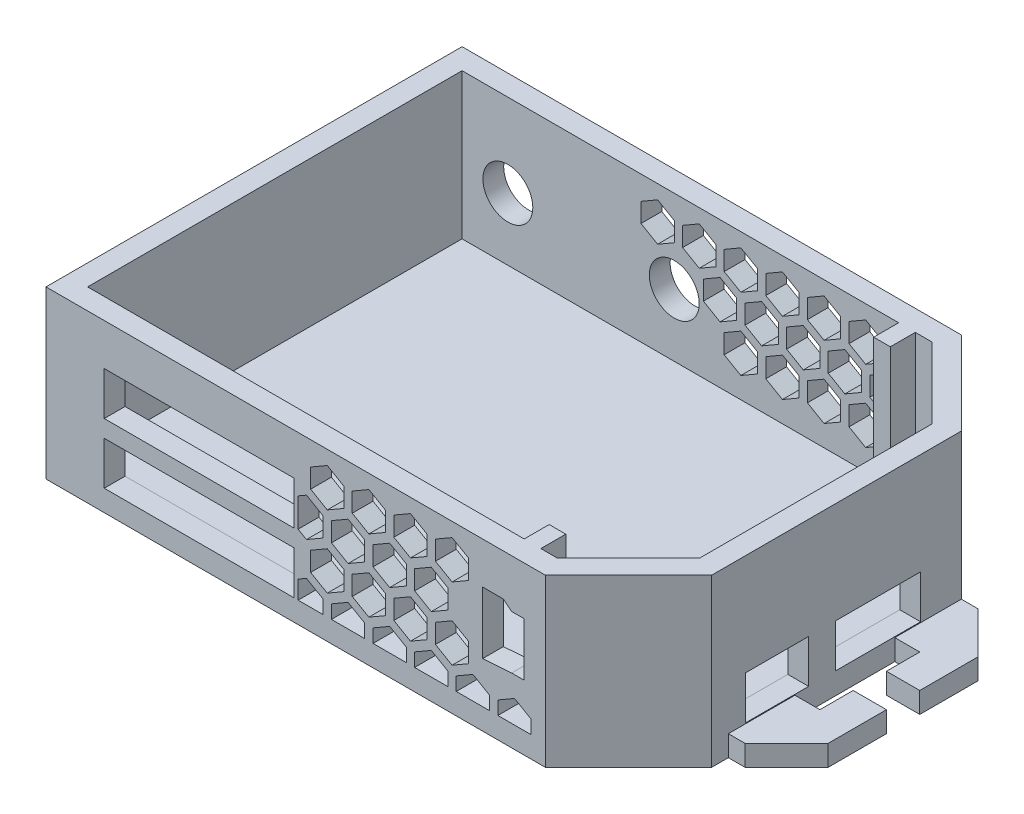
SolidWorks part; units mm, degrees
ref_plane "Front Plane" through (0, 0, 0) normal (0, 0, 1) x (1, 0, 0)
ref_plane "Top Plane" through (0, 0, 0) normal (0, 1, 0) x (1, 0, 0)
ref_plane "Right Plane" through (0, 0, 0) normal (1, 0, 0) x (0, 0, -1)
sketch "Sketch1" plane through (0, 0, 0) normal (0, 1, 0) x (1, 0, 0)
  line L1 (-35, 25) -> (35, 25)
  line L2 (-35, 25) -> (-35, -25)
  line L3 (-35, -25) -> (35, -25)
  line L4 (35, 25) -> (35, -25)
  line L5 (0, -25) -> (0, 25) construction
  line L6 (-35, 0) -> (35, 0) construction
  point P0 (0, 0)
  dimension "D1" = 70
  dimension "D2" = 50
extrude "Boss-Extrude1" add sketch "Sketch1" along normal blind 20
chamfer "Chamfer2" distance 10 angle 45 2 edges at (35, 10, 25) (35, 10, -25)
shell "Shell3" thickness 2.5
sketch "Sketch2" plane through (0, 0, -25) normal (0, 0, -1) x (-1, 0, 0)
  line L0 (-25, 0) -> (35, 0) construction
  line L1 (35, 20) -> (35, 0) construction
  circle A0 centre (27, 10) radius 3
  dimension "D1" = 6
  dimension "D2" = 10
  dimension "D3" = 8
extrude "Cut-Extrude1" cut sketch "Sketch2" against normal blind 20
sketch "Sketch3" plane through (0, 0, -22.5) normal (0, 0, 1) x (1, 0, 0)
  line L0 (23.9645, 2.5) -> (-32.5, 2.5) construction
  line L1 (21.9645, 2.5) -> (19.9645, 2.5)
  line L2 (21.9645, 2.5) -> (21.9645, 20)
  line L3 (21.9645, 20) -> (19.9645, 20)
  line L4 (19.9645, 2.5) -> (19.9645, 20)
  line L5 (23.9645, 20) -> (-32.5, 20) construction
  line L6 (23.9645, 20) -> (23.9645, 2.5) construction
  dimension "D1" = 2
  dimension "D2" = 2
extrude "Boss-Extrude2" add sketch "Sketch3" along normal blind 3
sketch "Sketch4" plane through (0, 0, 22.5) normal (0, 0, -1) x (-1, 0, 0)
  line L0 (32.5, 2.5) -> (-23.9645, 2.5) construction
  line L1 (-21.9645, 2.5) -> (-19.9645, 2.5)
  line L2 (-21.9645, 2.5) -> (-21.9645, 6.5)
  line L3 (-21.9645, 6.5) -> (-19.9645, 6.5)
  line L4 (-19.9645, 2.5) -> (-19.9645, 6.5)
  line L5 (-23.9645, 2.5) -> (-23.9645, 20) construction
  point P6 (-21.9645, 4.5)
  dimension "D1" = 2
  dimension "D2" = 4
  dimension "D3" = 2
extrude "Boss-Extrude3" add sketch "Sketch4" along normal blind 3
sketch "Sketch6" plane through (0, 0, 22.5) normal (0, 0, -1) x (-1, 0, 0)
  line L0 (32.5, 20) -> (-23.9645, 20) construction
  line L1 (-19.9645, 20) -> (-21.9645, 20)
  line L2 (-19.9645, 20) -> (-19.9645, 16)
  line L3 (-19.9645, 16) -> (-21.9645, 16)
  line L4 (-21.9645, 20) -> (-21.9645, 16)
  dimension "D1" = 4
  dimension "D2" = 2
  dimension "D3" = 2
extrude "Boss-Extrude4" add sketch "Sketch6" along normal blind 3
sketch "Sketch9" plane through (0, 0, 25) normal (0, 0, 1) x (1, 0, 0)
  line L0 (19.5, 14.5) -> (18.5, 13.7)
  line L1 (22, 14.5) -> (17, 14.5)
  line L2 (22, 14.5) -> (22, 6.5)
  line L3 (22, 6.5) -> (17, 6.5)
  line L4 (17, 14.5) -> (17, 6.5)
  line L5 (18.5, 13.7) -> (17, 13.7)
  line L6 (19.5, 6.5) -> (18.5, 7.3)
  line L7 (18.5, 7.3) -> (17, 7.3)
  line L8 (-35, 0) -> (25, 0) construction
  line L9 (25, 0) -> (25, 20) construction
  point P10 (6.2655, 14.9626)
  point P12 (6.4121, 6.9626)
  dimension "D1" = 8
  dimension "D2" = 5
  dimension "D3" = 0.8
  dimension "D4" = 0.8
  dimension "D5" = 1.5
  dimension "D6" = 1.5
  dimension "D7" = 1
  dimension "D8" = 1
  dimension "D9" = 6.5
  dimension "D10" = 3
sketch "Sketch10" plane through (0, 0, 22.5) normal (0, 0, -1) x (-1, 0, 0)
  line L0 (-19.9645, 15) -> (-20.9645, 14.2)
  line L1 (-17.4645, 15) -> (-22.4645, 15)
  line L2 (-17.4645, 15) -> (-17.4645, 7)
  line L3 (-17.4645, 7) -> (-22.4645, 7)
  line L4 (-22.4645, 15) -> (-22.4645, 7)
  line L5 (-20.9645, 14.2) -> (-22.4645, 14.2)
  line L6 (-9.9645, 7) -> (-20.9645, 7.8)
  line L7 (-20.9645, 7.8) -> (-22.4645, 7.8)
  line L9 (-19.9645, 2.5) -> (-19.9645, 6.5) construction
  point P6 (-9.9645, 7)
  point P10 (-5.6953, 16.1153)
  point P12 (-5.5488, 8.1153)
  dimension "D1" = 8
  dimension "D2" = 5
  dimension "D3" = 0.8
  dimension "D4" = 0.8
  dimension "D5" = 1.5
  dimension "D6" = 1.5
  dimension "D7" = 1
  dimension "D9" = 2.5
  dimension "D10" = 0.5
extrude "Cut-Extrude4" cut sketch "Sketch10" against normal blind 3 contours L7 L6 L3 L2 L1 L0 L5 L4
sketch "Sketch11" plane through (0, 0, 25) normal (0, 0, 1) x (1, 0, 0)
  line L0 (-35, 20) -> (-35, 0) construction
  line L1 (-28, 15) -> (-5.2, 15)
  line L2 (-28, 15) -> (-28, 9.8)
  line L3 (-28, 9.8) -> (-5.2, 9.8)
  line L4 (-5.2, 15) -> (-5.2, 9.8)
  line L5 (-35, 20) -> (25, 20) construction
  line L6 (-28, 12.4) -> (-5.2, 12.4) construction
  line L7 (-28, 7.746) -> (-5.2, 7.746)
  line L8 (-28, 7.746) -> (-28, 2.546)
  line L9 (-28, 2.546) -> (-5.2, 2.546)
  line L10 (-5.2, 7.746) -> (-5.2, 2.546)
  line L11 (-28, 5.146) -> (-5.2, 5.146) construction
  point P8 (-5, 20)
  dimension "D1" = 22.8
  dimension "D2" = 5.2
  dimension "D3" = 7
  dimension "D4" = 5
  dimension "D5" = 5.2
  dimension "D6" = 7.254
  dimension "D7" = 22.8
  dimension "D8" = 7
extrude "Cut-Extrude5" cut sketch "Sketch11" against normal blind 4
sketch "Sketch12" plane through (35, 0, 0) normal (1, 0, 0) x (0, 0, -1)
  line L0 (-15, 0) -> (15, 0) construction
  line L1 (-10.9521, 7.8) -> (-3.3521, 7.8)
  line L2 (-10.9521, 7.8) -> (-10.9521, 2.6)
  line L3 (-10.9521, 2.6) -> (-3.3521, 2.6)
  line L4 (-3.3521, 7.8) -> (-3.3521, 2.6)
  dimension "D1" = 2.6
  dimension "D2" = 7.6
  dimension "D3" = 5.2
extrude "Cut-Extrude6" cut sketch "Sketch12" against normal blind 4
sketch "Sketch13" plane through (35, 0, 0) normal (1, 0, 0) x (0, 0, -1)
  line L0 (-3.3521, 2.6) -> (-3.3521, 7.8) construction
  line L1 (-0.1021, 7.8) -> (10.0979, 7.8)
  line L2 (-0.1021, 7.8) -> (-0.1021, 2.6)
  line L3 (-0.1021, 2.6) -> (10.0979, 2.6)
  line L4 (10.0979, 7.8) -> (10.0979, 2.6)
  line L5 (-15, 0) -> (15, 0) construction
  dimension "D1" = 3.25
  dimension "D2" = 5.2
  dimension "D3" = 2.6
  dimension "D4" = 10.2
extrude "Cut-Extrude7" cut sketch "Sketch13" against normal blind 4
sketch "Sketch18" plane through (-35, 0, 0) normal (-1, 0, 0) x (0, 0, 1)
  line L0 (-25, 0) -> (25, 0) construction
  line L1 (-15, 0) -> (-7, 0)
  line L2 (-15, 0) -> (-15, 2.5)
  line L3 (-15, 2.5) -> (-7, 2.5)
  line L4 (-7, 0) -> (-7, 2.5)
  line L5 (-25, 20) -> (-25, 0) construction
  line L7 (5, 0) -> (13, 0)
  line L8 (5, 0) -> (5, 2.5)
  line L9 (5, 2.5) -> (13, 2.5)
  line L10 (13, 0) -> (13, 2.5)
  point P12 (-7, 1.25)
  dimension "D1" = 2.5
  dimension "D2" = 8
  dimension "D3" = 10
  dimension "D4" = 8
  dimension "D5" = 12
extrude "Boss-Extrude5" add sketch "Sketch18" along normal blind 7
sketch "Sketch19" plane through (0, 0, -7) normal (0, 0, 1) x (1, 0, 0)
  line L0 (-42, 0) -> (-35, 0) construction
  line L1 (-42, 2.5) -> (-38, 2.5)
  line L2 (-42, 2.5) -> (-42, 0)
  line L3 (-42, 0) -> (-38, 0)
  line L4 (-38, 2.5) -> (-38, 0)
  dimension "D1" = 4
extrude "Boss-Extrude6" add sketch "Sketch19" along normal blind 4
sketch "Sketch20" plane through (0, 0, 5) normal (0, 0, -1) x (-1, 0, 0)
  line L0 (42, 2.5) -> (35, 2.5) construction
  line L1 (42, 0) -> (38, 0)
  line L2 (42, 0) -> (42, 2.5)
  line L3 (42, 2.5) -> (38, 2.5)
  line L4 (38, 0) -> (38, 2.5)
  dimension "D1" = 4
extrude "Boss-Extrude7" add sketch "Sketch20" along normal blind 4
chamfer "Chamfer3" distance 5 angle 45 2 edges at (-42, 1.25, -15) (-42, 1.25, 13)
sketch "Sketch23" plane through (35, 0, 0) normal (1, 0, 0) x (0, 0, -1)
  line L1 (-13, 0) -> (-5, 0)
  line L2 (-13, 0) -> (-13, 2.5)
  line L3 (-13, 2.5) -> (-5, 2.5)
  line L4 (-5, 0) -> (-5, 2.5)
  line L6 (25, 20) -> (25, 0) construction
  line L7 (7, 0) -> (15, 0)
  line L8 (7, 0) -> (7, 2.5)
  line L9 (7, 2.5) -> (15, 2.5)
  line L10 (15, 0) -> (15, 2.5)
  line L11 (-15, 0) -> (15, 0) construction
  point P4 (0, 0)
  point P12 (-5, 1.25)
  dimension "D1" = 2.5
  dimension "D2" = 8
  dimension "D3" = 10
  dimension "D4" = 8
  dimension "D5" = 12
  dimension "D6" = 2.5
  dimension "D7" = 0
extrude "Boss-Extrude8" add sketch "Sketch23" along normal blind 7
sketch "Sketch24" plane through (0, 0, -7) normal (0, 0, 1) x (1, 0, 0)
  line L0 (42, 2.5) -> (35, 2.5) construction
  line L1 (42, 0) -> (38, 0)
  line L2 (42, 0) -> (42, 2.5)
  line L3 (42, 2.5) -> (38, 2.5)
  line L4 (38, 0) -> (38, 2.5)
  dimension "D1" = 4
extrude "Boss-Extrude10" add sketch "Sketch24" along normal blind 4
sketch "Sketch25" plane through (0, 0, 5) normal (0, 0, -1) x (-1, 0, 0)
  line L0 (-42, 0) -> (-35, 0) construction
  line L1 (-42, 2.5) -> (-38, 2.5)
  line L2 (-42, 2.5) -> (-42, 0)
  line L3 (-42, 0) -> (-38, 0)
  line L4 (-38, 2.5) -> (-38, 0)
  dimension "D1" = 4
extrude "Boss-Extrude11" add sketch "Sketch25" along normal blind 4
chamfer "Chamfer4" distance 5 angle 45 2 edges at (42, 1.25, 13) (42, 1.25, -15)
sketch "Sketch26" plane through (0, 0, -25) normal (0, 0, -1) x (-1, 0, 0)
  line L0 (27, 10) -> (32.4685, 10) construction
  circle A0 centre (7, 10) radius 3
  dimension "D1" = 6
  dimension "D2" = 20
extrude "Cut-Extrude10" cut sketch "Sketch26" against normal blind 4
sketch "Sketch27" plane through (0, 0, 25) normal (0, 0, 1) x (1, 0, 0)
  line L2 (-35, 20) -> (25, 20) construction
  line L3 (3.8, 18.3094) -> (1.8, 17.1547)
  line L4 (1.8, 17.1547) -> (1.8, 14.8453)
  line L5 (5.8, 17.1547) -> (3.8, 18.3094)
  line L6 (5.8, 14.8453) -> (5.8, 17.1547)
  line L8 (3.8, 13.6906) -> (5.8, 14.8453)
  line L9 (1.8, 14.8453) -> (3.8, 13.6906)
  line L10 (8.8, 18.3094) -> (6.8, 17.1547)
  line L11 (6.8, 17.1547) -> (6.8, 14.8453)
  line L12 (10.8, 17.1547) -> (8.8, 18.3094)
  line L13 (10.8, 14.8453) -> (10.8, 17.1547)
  line L14 (8.8, 13.6906) -> (10.8, 14.8453)
  line L15 (6.8, 14.8453) -> (8.8, 13.6906)
  line L16 (13.8, 18.3094) -> (11.8, 17.1547)
  line L17 (11.8, 17.1547) -> (11.8, 14.8453)
  line L18 (15.8, 17.1547) -> (13.8, 18.3094)
  line L19 (15.8, 14.8453) -> (15.8, 17.1547)
  line L20 (13.8, 13.6906) -> (15.8, 14.8453)
  line L21 (11.8, 14.8453) -> (13.8, 13.6906)
  line L22 (1.3, 13.9793) -> (-0.7, 12.8246)
  line L23 (-0.7, 12.8246) -> (-0.7, 10.5152)
  line L24 (3.3, 12.8246) -> (1.3, 13.9793)
  line L25 (3.3, 10.5152) -> (3.3, 12.8246)
  line L26 (1.3, 9.3605) -> (3.3, 10.5152)
  line L27 (0.8, 17.1547) -> (-1.2, 18.3094)
  line L28 (-1.2, 18.3094) -> (-3.2, 17.1547)
  line L29 (-3.2, 17.1547) -> (-3.2, 14.8453)
  line L30 (-3.2, 14.8453) -> (-1.2, 13.6906)
  line L31 (-1.2, 13.6906) -> (0.8, 14.8453)
  line L32 (0.8, 14.8453) -> (0.8, 17.1547)
  line L33 (-0.7, 10.5152) -> (1.3, 9.3605)
  line L34 (6.3, 13.9793) -> (4.3, 12.8246)
  line L35 (4.3, 12.8246) -> (4.3, 10.5152)
  line L36 (4.3, 10.5152) -> (6.3, 9.3605)
  line L37 (6.3, 9.3605) -> (8.3, 10.5152)
  line L38 (8.3, 10.5152) -> (8.3, 12.8246)
  line L39 (8.3, 12.8246) -> (6.3, 13.9793)
  line L40 (11.3, 13.9793) -> (9.3, 12.8246)
  line L41 (9.3, 12.8246) -> (9.3, 10.5152)
  line L42 (9.3, 10.5152) -> (11.3, 9.3605)
  line L43 (11.3, 9.3605) -> (13.3, 10.5152)
  line L44 (13.3, 10.5152) -> (13.3, 12.8246)
  line L45 (13.3, 12.8246) -> (11.3, 13.9793)
  line L46 (16.3, 13.9793) -> (14.3, 12.8246)
  line L47 (14.3, 12.8246) -> (14.3, 10.5152)
  line L48 (14.3, 10.5152) -> (16.3, 9.3605)
  line L49 (16.3, 9.3605) -> (18.3, 10.5152)
  line L50 (18.3, 12.8246) -> (16.3, 13.9793)
  line L51 (18.3, 10.5152) -> (18.3, 12.8246)
  line L52 (3.8, 9.6491) -> (1.8, 8.4944)
  line L53 (1.8, 8.4944) -> (1.8, 6.185)
  line L54 (5.8, 8.4944) -> (3.8, 9.6491)
  line L55 (5.8, 6.185) -> (5.8, 8.4944)
  line L56 (3.8, 5.0303) -> (5.8, 6.185)
  line L57 (1.8, 6.185) -> (3.8, 5.0303)
  line L58 (8.8, 9.6491) -> (6.8, 8.4944)
  line L59 (6.8, 8.4944) -> (6.8, 6.185)
  line L60 (6.8, 6.185) -> (8.8, 5.0303)
  line L61 (8.8, 5.0303) -> (10.8, 6.185)
  line L62 (10.8, 6.185) -> (10.8, 8.4944)
  line L63 (10.8, 8.4944) -> (8.8, 9.6491)
  line L64 (13.8, 9.6491) -> (11.8, 8.4944)
  line L65 (11.8, 8.4944) -> (11.8, 6.185)
  line L66 (11.8, 6.185) -> (13.8, 5.0303)
  line L67 (13.8, 5.0303) -> (15.8, 6.185)
  line L68 (15.8, 6.185) -> (15.8, 8.4944)
  line L69 (15.8, 8.4944) -> (13.8, 9.6491)
  line L70 (18.8, 9.6491) -> (16.8, 8.4944)
  line L71 (16.8, 8.4944) -> (16.8, 6.185)
  line L72 (16.8, 6.185) -> (18.8, 5.0303)
  line L73 (18.8, 5.0303) -> (20.8, 6.185)
  line L74 (20.8, 8.4944) -> (18.8, 9.6491)
  line L75 (20.8, 6.185) -> (20.8, 8.4944)
  line L76 (6.3, 5.319) -> (4.3, 4.1643)
  line L77 (4.3, 4.1643) -> (4.3, 1.8549)
  line L78 (8.3, 4.1643) -> (6.3, 5.319)
  line L79 (8.3, 1.8549) -> (8.3, 4.1643)
  line L80 (6.3, 0.7002) -> (8.3, 1.8549)
  line L81 (4.3, 1.8549) -> (6.3, 0.7002)
  line L82 (11.3, 5.319) -> (9.3, 4.1643)
  line L83 (9.3, 4.1643) -> (9.3, 1.8549)
  line L84 (9.3, 1.8549) -> (11.3, 0.7002)
  line L85 (11.3, 0.7002) -> (13.3, 1.8549)
  line L86 (13.3, 1.8549) -> (13.3, 4.1643)
  line L87 (13.3, 4.1643) -> (11.3, 5.319)
  line L88 (16.3, 5.319) -> (14.3, 4.1643)
  line L89 (14.3, 4.1643) -> (14.3, 1.8549)
  line L90 (14.3, 1.8549) -> (16.3, 0.7002)
  line L91 (16.3, 0.7002) -> (18.3, 1.8549)
  line L92 (18.3, 1.8549) -> (18.3, 4.1643)
  line L93 (18.3, 4.1643) -> (16.3, 5.319)
  line L94 (21.3, 5.319) -> (19.3, 4.1643)
  line L95 (19.3, 4.1643) -> (19.3, 1.8549)
  line L96 (19.3, 1.8549) -> (21.3, 0.7002)
  line L97 (21.3, 0.7002) -> (23.3, 1.8549)
  line L98 (23.3, 4.1643) -> (21.3, 5.319)
  line L99 (23.3, 1.8549) -> (23.3, 4.1643)
  line L100 (8.8, 0.9889) -> (6.8, -0.1658)
  line L101 (6.8, -0.1658) -> (6.8, -2.4752)
  line L102 (10.8, -0.1658) -> (8.8, 0.9889)
  line L103 (10.8, -2.4752) -> (10.8, -0.1658)
  line L104 (8.8, -3.6299) -> (10.8, -2.4752)
  line L105 (6.8, -2.4752) -> (8.8, -3.6299)
  line L106 (13.8, 0.9889) -> (11.8, -0.1658)
  line L107 (11.8, -0.1658) -> (11.8, -2.4752)
  line L108 (11.8, -2.4752) -> (13.8, -3.6299)
  line L109 (13.8, -3.6299) -> (15.8, -2.4752)
  line L110 (15.8, -2.4752) -> (15.8, -0.1658)
  line L111 (15.8, -0.1658) -> (13.8, 0.9889)
  line L112 (18.8, 0.9889) -> (16.8, -0.1658)
  line L113 (16.8, -0.1658) -> (16.8, -2.4752)
  line L114 (16.8, -2.4752) -> (18.8, -3.6299)
  line L115 (18.8, -3.6299) -> (20.8, -2.4752)
  line L116 (20.8, -2.4752) -> (20.8, -0.1658)
  line L117 (20.8, -0.1658) -> (18.8, 0.9889)
  line L118 (23.8, 0.9889) -> (21.8, -0.1658)
  line L119 (21.8, -0.1658) -> (21.8, -2.4752)
  line L120 (21.8, -2.4752) -> (23.8, -3.6299)
  line L121 (23.8, -3.6299) -> (25.8, -2.4752)
  line L122 (25.8, -0.1658) -> (23.8, 0.9889)
  line L123 (25.8, -2.4752) -> (25.8, -0.1658)
  line L124 (-3.7, 9.3605) -> (-1.7, 10.5152)
  line L125 (-5.7, 10.5152) -> (-3.7, 9.3605)
  line L126 (-5.7, 12.8246) -> (-5.7, 10.5152)
  line L127 (-3.7, 13.9793) -> (-5.7, 12.8246)
  line L128 (-1.7, 12.8246) -> (-3.7, 13.9793)
  line L129 (-1.7, 10.5152) -> (-1.7, 12.8246)
  line L130 (-0.7, 4.1643) -> (-0.7, 1.8549)
  line L131 (1.3, 5.319) -> (-0.7, 4.1643)
  line L132 (3.3, 4.1643) -> (1.3, 5.319)
  line L133 (3.3, 1.8549) -> (3.3, 4.1643)
  line L134 (1.3, 0.7002) -> (3.3, 1.8549)
  line L135 (-0.7, 1.8549) -> (1.3, 0.7002)
  line L136 (-3.2, 6.185) -> (-1.2, 5.0303)
  line L137 (-3.2, 8.4944) -> (-3.2, 6.185)
  line L138 (-1.2, 9.6491) -> (-3.2, 8.4944)
  line L139 (0.8, 8.4944) -> (-1.2, 9.6491)
  line L140 (0.8, 6.185) -> (0.8, 8.4944)
  line L141 (-1.2, 5.0303) -> (0.8, 6.185)
  line L142 (-3.2, -0.1658) -> (-3.2, -2.4752)
  line L143 (-1.2, 0.9889) -> (-3.2, -0.1658)
  line L144 (0.8, -0.1658) -> (-1.2, 0.9889)
  line L145 (0.8, -2.4752) -> (0.8, -0.1658)
  line L146 (-1.2, -3.6299) -> (0.8, -2.4752)
  line L147 (-3.2, -2.4752) -> (-1.2, -3.6299)
  line L148 (-5.7, 1.8549) -> (-3.7, 0.7002)
  line L149 (-5.7, 4.1643) -> (-5.7, 1.8549)
  line L150 (-3.7, 5.319) -> (-5.7, 4.1643)
  line L151 (-1.7, 4.1643) -> (-3.7, 5.319)
  line L152 (-1.7, 1.8549) -> (-1.7, 4.1643)
  line L153 (-3.7, 0.7002) -> (-1.7, 1.8549)
  line L154 (-5.7, 2.546) -> (23.3, 2.546)
  line L155 (-28, 2.546) -> (-5.2, 2.546) construction
  line L156 (-4.7, 13.4019) -> (-4.7, 2.546)
  circle A1 centre (-1.2, 16) radius 2 construction
  dimension "D2" = 4
  dimension "D1" = 4
  dimension "D3" = 4
  dimension "D5" = 5
  dimension "D4" = 4
extrude "Cut-Extrude11" cut sketch "Sketch27" against normal blind 4 contours L150 L156 L154 L152 L151 | L130 L154 L133 L132 L131 | L136 L141 L140 L139 L138 L137 | L53 L57 L56 L55 L54 L52 | L77 L154 L79 L78 L76 | L83 L154 L86 L87 L82 | L62 L63 L58 L59 L60 L61 | L68 L69 L64 L65 L66 L67 | L89 L154 L92 L93 L88 | L95 L154 L99 L98 L94 | L44 L45 L40 L41 L42 L43 | L17 L21 L20 L19 L18 L16 | L11 L15 L14 L13 L12 L10 | L38 L39 L34 L35 L36 L37 | L4 L9 L8 L6 L5 L3 | L23 L33 L26 L25 L24 L22 | L127 L156 L125 L124 L129 L128 | L31 L32 L27 L28 L29 L30
sketch "Sketch33" plane through (0, 0, -25) normal (0, 0, -1) x (-1, 0, 0)
  line L0 (-25, 20) -> (35, 20) construction
  line L1 (-25, 20) -> (-25, 0) construction
  line L2 (4, 18.3094) -> (2, 17.1547)
  line L3 (-16, 18.3094) -> (-18, 17.1547)
  line L4 (-18, 17.1547) -> (-18, 14.8453)
  line L5 (-14, 17.1547) -> (-16, 18.3094)
  line L6 (-14, 14.8453) -> (-14, 17.1547)
  line L7 (2, 17.1547) -> (2, 14.8453)
  line L8 (-16, 13.6906) -> (-14, 14.8453)
  line L9 (-18, 14.8453) -> (-16, 13.6906)
  line L10 (-11, 18.3094) -> (-13, 17.1547)
  line L11 (-13, 17.1547) -> (-13, 14.8453)
  line L12 (-9, 17.1547) -> (-11, 18.3094)
  line L13 (-9, 14.8453) -> (-9, 17.1547)
  line L14 (-11, 13.6906) -> (-9, 14.8453)
  line L15 (-13, 14.8453) -> (-11, 13.6906)
  line L16 (-6, 18.3094) -> (-8, 17.1547)
  line L17 (-8, 17.1547) -> (-8, 14.8453)
  line L18 (-4, 17.1547) -> (-6, 18.3094)
  line L19 (-4, 14.8453) -> (-4, 17.1547)
  line L20 (-6, 13.6906) -> (-4, 14.8453)
  line L21 (-8, 14.8453) -> (-6, 13.6906)
  line L22 (6, 17.1547) -> (4, 18.3094)
  line L23 (6, 14.8453) -> (6, 17.1547)
  line L24 (4, 13.6906) -> (6, 14.8453)
  line L25 (2, 14.8453) -> (4, 13.6906)
  line L26 (9, 18.3094) -> (7, 17.1547)
  line L27 (-19, 17.1547) -> (-21, 18.3094)
  line L28 (-21, 18.3094) -> (-23, 17.1547)
  line L29 (-23, 17.1547) -> (-23, 14.8453)
  line L30 (-23, 14.8453) -> (-21, 13.6906)
  line L31 (-21, 13.6906) -> (-19, 14.8453)
  line L33 (7, 17.1547) -> (7, 14.8453)
  line L34 (11, 17.1547) -> (9, 18.3094)
  line L35 (11, 14.8453) -> (11, 17.1547)
  line L36 (9, 13.6906) -> (11, 14.8453)
  line L37 (7, 14.8453) -> (9, 13.6906)
  line L44 (1, 17.1547) -> (-1, 18.3094)
  line L45 (-1, 18.3094) -> (-3, 17.1547)
  line L46 (-3, 17.1547) -> (-3, 14.8453)
  line L47 (-3, 14.8453) -> (-1, 13.6906)
  line L48 (-1, 13.6906) -> (1, 14.8453)
  line L49 (1, 14.8453) -> (1, 17.1547)
  line L50 (1.5, 13.9793) -> (-0.5, 12.8246)
  line L51 (-18.5, 13.9793) -> (-20.5, 12.8246)
  line L52 (-20.5, 12.8246) -> (-20.5, 10.5152)
  line L53 (-16.5, 12.8246) -> (-18.5, 13.9793)
  line L54 (-16.5, 10.5152) -> (-16.5, 12.8246)
  line L55 (-0.5, 12.8246) -> (-0.5, 10.5152)
  line L56 (-18.5, 9.3605) -> (-16.5, 10.5152)
  line L57 (-20.5, 10.5152) -> (-18.5, 9.3605)
  line L58 (-13.5, 13.9793) -> (-15.5, 12.8246)
  line L59 (-15.5, 12.8246) -> (-15.5, 10.5152)
  line L60 (-11.5, 12.8246) -> (-13.5, 13.9793)
  line L61 (-11.5, 10.5152) -> (-11.5, 12.8246)
  line L62 (-13.5, 9.3605) -> (-11.5, 10.5152)
  line L63 (-15.5, 10.5152) -> (-13.5, 9.3605)
  line L64 (-8.5, 13.9793) -> (-10.5, 12.8246)
  line L65 (-10.5, 12.8246) -> (-10.5, 10.5152)
  line L66 (-6.5, 12.8246) -> (-8.5, 13.9793)
  line L67 (-6.5, 10.5152) -> (-6.5, 12.8246)
  line L68 (-8.5, 9.3605) -> (-6.5, 10.5152)
  line L69 (-10.5, 10.5152) -> (-8.5, 9.3605)
  line L70 (3.5, 12.8246) -> (1.5, 13.9793)
  line L71 (3.5, 10.5152) -> (3.5, 12.8246)
  line L72 (1.5, 9.3605) -> (3.5, 10.5152)
  line L73 (-0.5, 10.5152) -> (1.5, 9.3605)
  line L92 (-1.5, 12.8246) -> (-3.5, 13.9793)
  line L93 (-3.5, 13.9793) -> (-5.5, 12.8246)
  line L94 (-5.5, 12.8246) -> (-5.5, 10.5152)
  line L95 (-5.5, 10.5152) -> (-3.5, 9.3605)
  line L96 (-3.5, 9.3605) -> (-1.5, 10.5152)
  line L97 (-1.5, 10.5152) -> (-1.5, 12.8246)
  line L99 (-16, 9.6491) -> (-18, 8.4944)
  line L100 (-18, 8.4944) -> (-18, 6.185)
  line L101 (-14, 8.4944) -> (-16, 9.6491)
  line L102 (-14, 6.185) -> (-14, 8.4944)
  line L104 (-16, 5.0303) -> (-14, 6.185)
  line L105 (-18, 6.185) -> (-16, 5.0303)
  line L106 (-11, 9.6491) -> (-13, 8.4944)
  line L107 (-13, 8.4944) -> (-13, 6.185)
  line L108 (-9, 8.4944) -> (-11, 9.6491)
  line L109 (-9, 6.185) -> (-9, 8.4944)
  line L110 (-11, 5.0303) -> (-9, 6.185)
  line L111 (-13, 6.185) -> (-11, 5.0303)
  line L112 (-6, 9.6491) -> (-8, 8.4944)
  line L113 (-8, 8.4944) -> (-8, 6.185)
  line L114 (-4, 8.4944) -> (-6, 9.6491)
  line L115 (-4, 6.185) -> (-4, 8.4944)
  line L116 (-6, 5.0303) -> (-4, 6.185)
  line L117 (-8, 6.185) -> (-6, 5.0303)
  line L123 (-19, 8.4944) -> (-21, 9.6491)
  line L124 (-21, 9.6491) -> (-23, 8.4944)
  line L125 (-23, 8.4944) -> (-23, 6.185)
  line L126 (-23, 6.185) -> (-21, 5.0303)
  line L127 (-21, 5.0303) -> (-19, 6.185)
  line L140 (1, 8.4944) -> (-1, 9.6491)
  line L141 (-1, 9.6491) -> (-3, 8.4944)
  line L142 (-3, 8.4944) -> (-3, 6.185)
  line L143 (-3, 6.185) -> (-1, 5.0303)
  line L144 (-1, 5.0303) -> (1, 6.185)
  line L145 (1, 6.185) -> (1, 8.4944)
  line L263 (8.5, 12.8246) -> (6.5, 13.9793) [skipped]
  line L264 (6.5, 13.9793) -> (4.5, 12.8246) [skipped]
  line L265 (8.5, 10.5152) -> (8.5, 12.8246) [skipped]
  line L266 (6.5, 9.3605) -> (8.5, 10.5152) [skipped]
  line L267 (4.5, 10.5152) -> (6.5, 9.3605) [skipped]
  line L268 (4.5, 12.8246) -> (4.5, 10.5152) [skipped]
  line L269 (6, 6.185) -> (6, 8.4944) [skipped]
  line L270 (6, 8.4944) -> (4, 9.6491) [skipped]
  line L271 (4, 9.6491) -> (2, 8.4944) [skipped]
  line L272 (2, 8.4944) -> (2, 6.185) [skipped]
  line L273 (2, 6.185) -> (4, 5.0303) [skipped]
  line L274 (4, 5.0303) -> (6, 6.185) [skipped]
  line L281 (12, 14.8453) -> (14, 13.6906) [skipped]
  line L282 (14, 18.3094) -> (12, 17.1547) [skipped]
  line L283 (12, 17.1547) -> (12, 14.8453) [skipped]
  line L284 (16, 17.1547) -> (14, 18.3094) [skipped]
  line L285 (16, 14.8453) -> (16, 17.1547) [skipped]
  line L286 (14, 13.6906) -> (16, 14.8453) [skipped]
  line L288 (-21.5, 12.8246) -> (-23.5, 13.9793) [skipped]
  line L289 (-23.5, 13.9793) -> (-25.5, 12.8246) [skipped]
  line L290 (-25.5, 12.8246) -> (-25.5, 10.5152) [skipped]
  line L291 (-25.5, 10.5152) -> (-23.5, 9.3605) [skipped]
  line L292 (-23.5, 9.3605) -> (-21.5, 10.5152) [skipped]
  line L293 (-19, 14.8453) -> (-19, 17.1547) [skipped]
  circle A0 centre (-1, 16) radius 2 construction
  circle A1 centre (-21, 16) radius 2 construction
  circle A2 centre (-3.5, 11.6699) radius 2 construction
  circle A4 centre (-1, 7.3397) radius 2 construction
  circle A5 centre (-21, 7.3397) radius 2 construction
  circle A6 centre (-23.5, 11.6699) radius 2 construction
  point P23 (0, 0)
  point P24 (0, 0)
  point P83 (0, 0)
  point P162 (0, 0)
  point P163 (0, 0)
  point P164 (0, 0)
  point P165 (0, 0)
  point P166 (0, 0)
  dimension "D2" = 4
  dimension "D1" = 4
  dimension "D3" = 4
  dimension "D6" = 2
  dimension "D5" = 2
  dimension "D4" = 4
  dimension "D7" = 2
extrude "Cut-Extrude13" cut sketch "Sketch33" against normal blind 4 contours L55 L73 L72 L71 L70 L50 | L7 L25 L24 L23 L22 L2 | L33 L37 L36 L35 L34 L26 | L48 L49 L44 L45 L46 L47 | L96 L97 L92 L93 L94 L95 | L144 L145 L140 L141 L142 L143 | L113 L117 L116 L115 L114 L112 | L65 L69 L68 L67 L66 L64 | L17 L21 L20 L19 L18 L16 | L11 L15 L14 L13 L12 L10 | L59 L63 L62 L61 L60 L58 | L4 L9 L8 L6 L5 L3 | L52 L57 L56 L54 L53 L51 | L100 L105 L104 L102 L101 L99 | L107 L111 L110 L109 L108 L106
